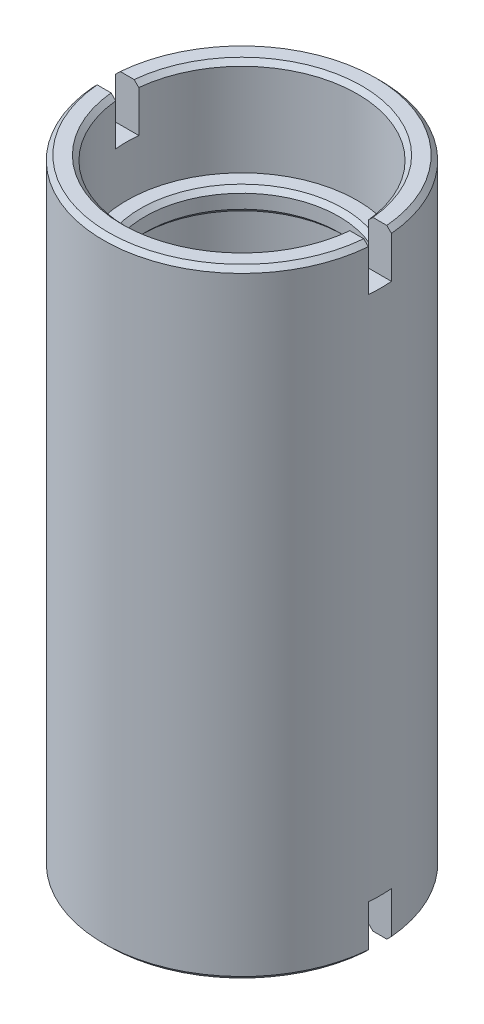
SolidWorks part; units mm, degrees
material "PA Type 6"
ref_plane "Front Plane" through (0, 0, 0) normal (0, 0, 1) x (1, 0, 0)
ref_plane "Top Plane" through (0, 0, 0) normal (0, 1, 0) x (1, 0, 0)
ref_plane "Right Plane" through (0, 0, 0) normal (1, 0, 0) x (0, 0, -1)
sketch "Sketch1" plane through (0, 0, 0) normal (0, 0, 1) x (1, 0, 0)
  line L0 (0, 0) -> (0, 27.3374) construction
  line L1 (25, -134) -> (30, -134)
  line L2 (30, -134) -> (30, 0)
  line L5 (30, 0) -> (25, 0)
  line L8 (25, 0) -> (25, -21)
  line L19 (25, -26) -> (25, -134)
  line L20 (25, -21) -> (21, -21)
  line L22 (25, -26) -> (21, -26)
  line L23 (21, -21) -> (21, -26)
  dimension "D1" = 5
  dimension "D2" = 134
  dimension "D3" = 5
  dimension "D4" = 4
  dimension "D5" = 26
  dimension "D6" = 30
revolve "Revolve1" add sketch "Sketch1" angle 360 about L0
sketch "Sketch2" plane through (0, 0, 0) normal (0, 1, 0) x (1, 0, 0)
  line L1 (-35, -2.5) -> (35, -2.5)
  line L2 (-35, -2.5) -> (-35, 2.5)
  line L3 (-35, 2.5) -> (35, 2.5)
  line L4 (35, -2.5) -> (35, 2.5)
  line L5 (-35, -2.5) -> (35, 2.5) construction
  line L6 (-35, 2.5) -> (35, -2.5) construction
  point P0 (0, 0)
  dimension "D1" = 5
  dimension "D2" = 70
extrude "Cut-Extrude1" cut sketch "Sketch2" against normal blind 10
sketch "Sketch3" plane through (0, -134, 0) normal (0, -1, 0) x (1, 0, 0)
  line L5 (-35, 2.5) -> (35, 2.5)
  line L6 (-35, 2.5) -> (-35, -2.5)
  line L7 (-35, -2.5) -> (35, -2.5)
  line L8 (35, 2.5) -> (35, -2.5)
  line L9 (-35, 2.5) -> (35, -2.5) construction
  line L10 (-35, -2.5) -> (35, 2.5) construction
  point P0 (0, 0)
  dimension "D1" = 5
  dimension "D2" = 70
extrude "Cut-Extrude2" cut sketch "Sketch3" against normal blind 10
chamfer "Chamfer1" distance 1 angle 45 10 edges at (0, -134, -30) (0, -134, -25) (0, -134, 30) (0, -134, 25) (0, -21, -21) (0, -26, -21) (0, 0, -25) (0, 0, -30) (0, 0, 25) (0, 0, 30)
